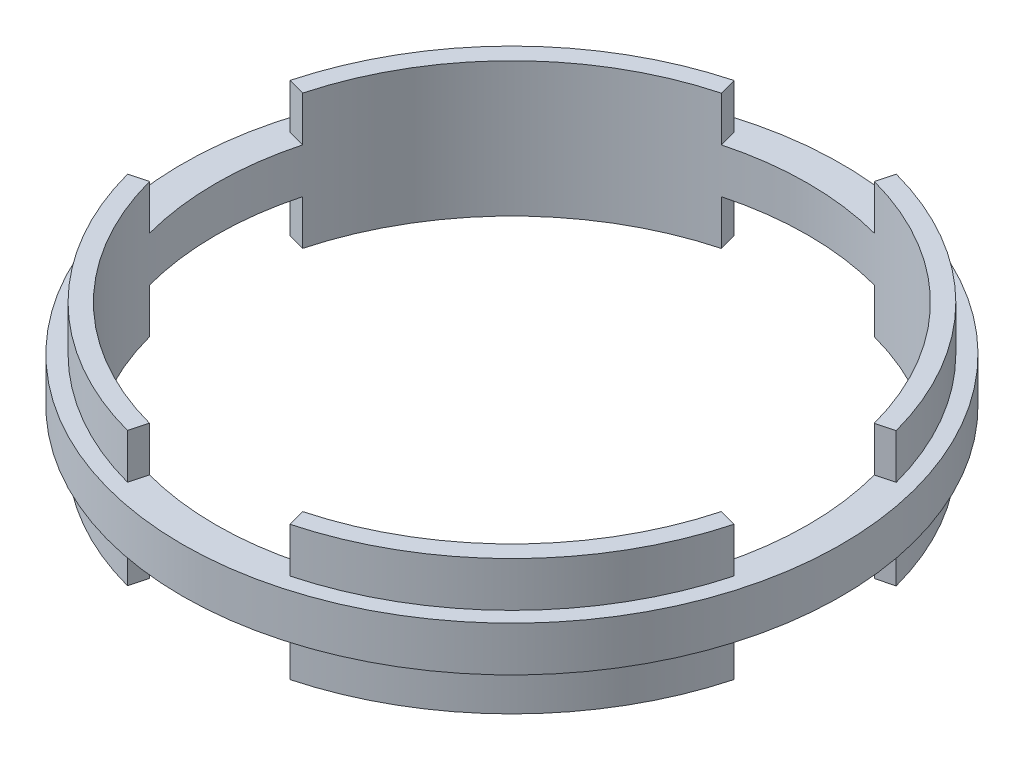
SolidWorks part; units mm, degrees
material "6061-T6 (SS)"
ref_plane "Front Plane" through (0, 0, 0) normal (0, 0, 1) x (1, 0, 0)
ref_plane "Top Plane" through (0, 0, 0) normal (0, 1, 0) x (1, 0, 0)
ref_plane "Right Plane" through (0, 0, 0) normal (1, 0, 0) x (0, 0, -1)
sketch "Sketch1" plane through (0, 0, 0) normal (0, 1, 0) x (1, 0, 0)
  circle A0 centre (0, 0) radius 93.345
  circle A1 centre (0, 0) radius 83.82
  dimension "D1" = 186.69
  dimension "D2" = 167.64
extrude "Boss-Extrude1" add sketch "Sketch1" along normal mid plane 12.7
sketch "Sketch2" plane through (0, 0, 0) normal (0, 1, 0) x (1, 0, 0)
  circle A0 centre (0, 0) radius 88.9
  circle A1 centre (0, 0) radius 83.82
  dimension "D1" = 177.8
  dimension "D2" = 167.64
extrude "Boss-Extrude2" add sketch "Sketch2" along normal mid plane 38.1
sketch "Sketch3" plane through (0, 0, 0) normal (0, 1, 0) x (1, 0, 0)
  line L0 (0, -116.3805) -> (0, 112.0878) construction
  line L1 (-120.9117, 0) -> (128.5432, 0) construction
  line L2 (0, 0) -> (-22.965, 85.8826)
  line L3 (0, 0) -> (23.009, 85.8708)
  circle A5 centre (0, 0) radius 88.9 construction
  arc A7 (-22.965, 85.8826) -> (23.009, 85.8708) centre (0, 0) cw
  dimension "D1" = 45.974
  dimension "D2" = 15
extrude "Cut-Extrude1" cut sketch "Sketch3" against normal mid plane 76.2
pattern_circular "CirPattern1" count 4 over 360 about axis through (0, 19.05, 0) along (0, -1, 0) of "Cut-Extrude1"
sketch "Sketch4" plane through (0, 0, 0) normal (0, 1, 0) x (1, 0, 0)
  circle A0 centre (0, 0) radius 88.9
  circle A1 centre (0, 0) radius 83.82
extrude "Boss-Extrude3" add sketch "Sketch4" along normal mid plane 12.7
